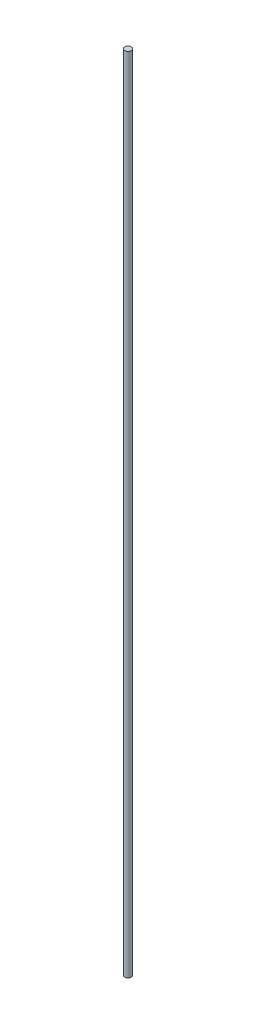
SolidWorks part; units mm, degrees
ref_plane "Front Plane" through (0, 0, 0) normal (0, 0, 1) x (1, 0, 0)
ref_plane "Top Plane" through (0, 0, 0) normal (0, 1, 0) x (1, 0, 0)
ref_plane "Right Plane" through (0, 0, 0) normal (1, 0, 0) x (0, 0, -1)
sketch "Sketch1" plane through (0, 0, 0) normal (0, 1, 0) x (1, 0, 0)
  circle A0 centre (0, 0) radius 3.175
  dimension "D1" = 6.35
extrude "Boss-Extrude1" add sketch "Sketch1" along normal mid plane 774.7
